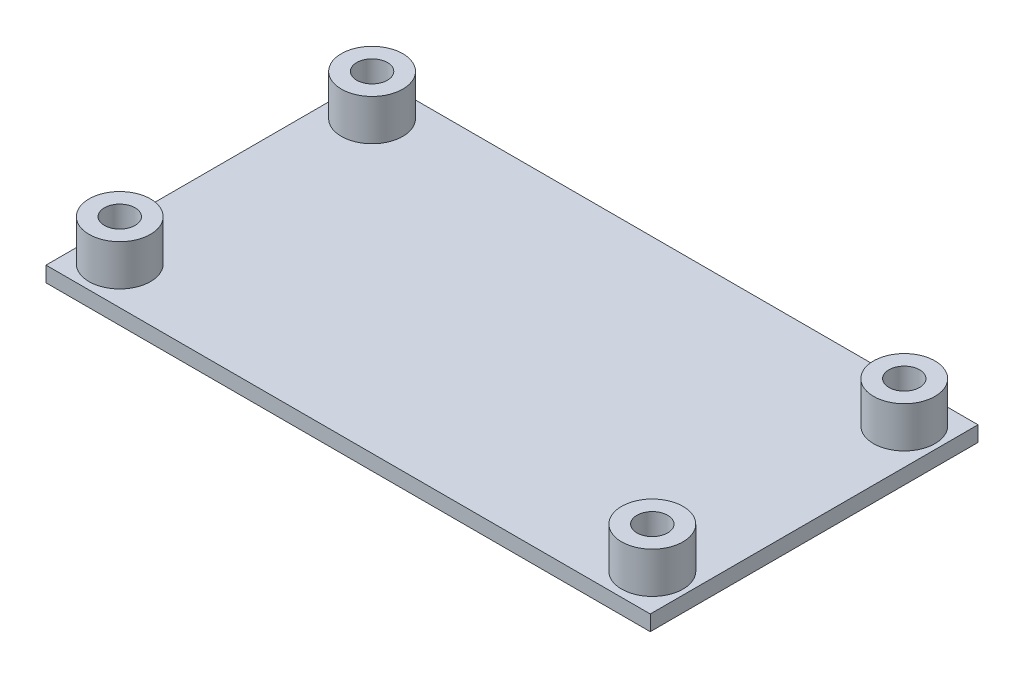
SolidWorks part; units mm, degrees
material "ABS PC"
ref_plane "前视基准面" through (0, 0, 0) normal (0, 0, 1) x (1, 0, 0)
ref_plane "上视基准面" through (0, 0, 0) normal (0, 1, 0) x (1, 0, 0)
ref_plane "右视基准面" through (0, 0, 0) normal (1, 0, 0) x (0, 0, -1)
sketch "草图2" plane through (0, 0, 0) normal (0, 1, 0) x (1, 0, 0)
  line L1 (-24.6381, 15.6657) -> (32.3619, 15.6657)
  line L2 (-24.6381, 15.6657) -> (-24.6381, -24.7343)
  line L3 (-24.6381, -24.7343) -> (32.3619, -24.7343)
  line L4 (32.3619, 15.6657) -> (32.3619, -24.7343)
  dimension "D1" = 57
  dimension "D2" = 40.4
extrude "凸台-拉伸1" add sketch "草图2" along normal blind 1.5
sketch "草图4" plane through (0, 1.5, 0) normal (0, 1, 0) x (1, 0, 0)
  line L0 (-24.6381, 15.6657) -> (-24.6381, -24.7343) construction
  circle A0 centre (-22.0994, 7.7657) radius 1.5
  circle A1 centre (-22.1381, 7.7657) radius 1.5 construction
  circle A2 centre (-22.0994, 7.7657) radius 3
  circle A3 centre (-22.1381, -16.8343) radius 1.5
  circle A4 centre (-22.1381, -16.8343) radius 1.5 construction
  circle A5 centre (-22.1381, -16.8343) radius 3
  circle A9 centre (29.8619, -16.8343) radius 1.5
  circle A10 centre (29.8619, -16.8343) radius 1.5 construction
  circle A11 centre (29.8619, -16.8343) radius 3
  circle A14 centre (29.8619, 7.7657) radius 1.5
  circle A15 centre (29.8619, 7.7657) radius 1.5 construction
  circle A16 centre (29.8619, 7.7657) radius 3
  dimension "D1" = 0
  dimension "D2" = 3
  dimension "D5" = 2.5387
  dimension "D6" = 6
  dimension "D7" = 0
  dimension "D8" = 3
  dimension "D9" = 6
  dimension "D10" = 0
  dimension "D11" = 3
  dimension "D12" = 6
  dimension "D13" = 0
  dimension "D14" = 6
  dimension "D15" = 3
  dimension "D3" = 0
  dimension "D4" = 2.5387
extrude "凸台-拉伸3" add sketch "草图4" along normal blind 4
sketch "草图5" plane through (0, 1.5, 0) normal (0, 1, 0) x (1, 0, 0)
  line L0 (32.3619, 15.6657) -> (-24.6381, 15.6657) construction
  line L1 (-24.6381, 15.6657) -> (32.3619, 15.6657)
  line L2 (-24.6381, 15.6657) -> (-24.6381, 11.4657)
  line L3 (-24.6381, 11.4657) -> (32.3619, 11.4657)
  line L4 (32.3619, 15.6657) -> (32.3619, 11.4657)
  line L5 (-24.6381, 15.6657) -> (-24.6381, 9.3641) construction
  line L6 (32.3619, 9.424) -> (32.3619, 15.6657) construction
  line L7 (32.3619, 10.6657) -> (-24.6381, 10.6657) construction
  line L8 (-24.6381, -18.4926) -> (-24.6381, -24.7343) construction
  line L9 (-24.6381, -20.5343) -> (32.3619, -20.5343)
  line L10 (-24.6381, -20.5343) -> (-24.6381, -24.7343)
  line L11 (-24.6381, -24.7343) -> (32.3619, -24.7343)
  line L12 (32.3619, -20.5343) -> (32.3619, -24.7343)
  line L13 (32.3619, -24.7343) -> (32.3619, -18.4926) construction
  line L14 (-24.6381, -24.7343) -> (32.3619, -24.7343) construction
  line L15 (-24.6381, -19.7343) -> (32.3619, -19.7343) construction
  dimension "D1" = 0
  dimension "D2" = 0
  dimension "D3" = 0
  dimension "D4" = 0.8
  dimension "D5" = 0
  dimension "D6" = 0
  dimension "D7" = 0
  dimension "D8" = 0.8
extrude "切除-拉伸1" cut sketch "草图5" against normal through all
sketch "草图6" plane through (0, 1.5, 0) normal (0, 1, 0) x (1, 0, 0)
  line L0 (-24.6381, 11.4657) -> (-24.6381, 9.3641) construction
  line L1 (-25.6381, 11.4657) -> (-24.6381, 11.4657)
  line L2 (-25.6381, 11.4657) -> (-25.6381, -20.5343)
  line L3 (-25.6381, -20.5343) -> (-24.6381, -20.5343)
  line L4 (-24.6381, 11.4657) -> (-24.6381, -20.5343)
  line L5 (-24.6381, 11.4657) -> (32.3619, 11.4657) construction
  line L6 (32.3619, -20.5343) -> (-24.6381, -20.5343) construction
  line L7 (32.3619, -15.176) -> (32.3619, 6.1074) construction
  line L8 (32.3619, 11.4657) -> (33.3619, 11.4657)
  line L9 (32.3619, 11.4657) -> (32.3619, -20.5343)
  line L10 (32.3619, -20.5343) -> (33.3619, -20.5343)
  line L11 (33.3619, 11.4657) -> (33.3619, -20.5343)
  dimension "D1" = 0
  dimension "D2" = 0
  dimension "D3" = 0
  dimension "D4" = 1
  dimension "D5" = 0
  dimension "D6" = 0
  dimension "D7" = 0
  dimension "D8" = 1
extrude "凸台-拉伸4" add sketch "草图6" against normal up to surface (1.5 mm away) up to face at (3.8619, 0, 4.5343)
